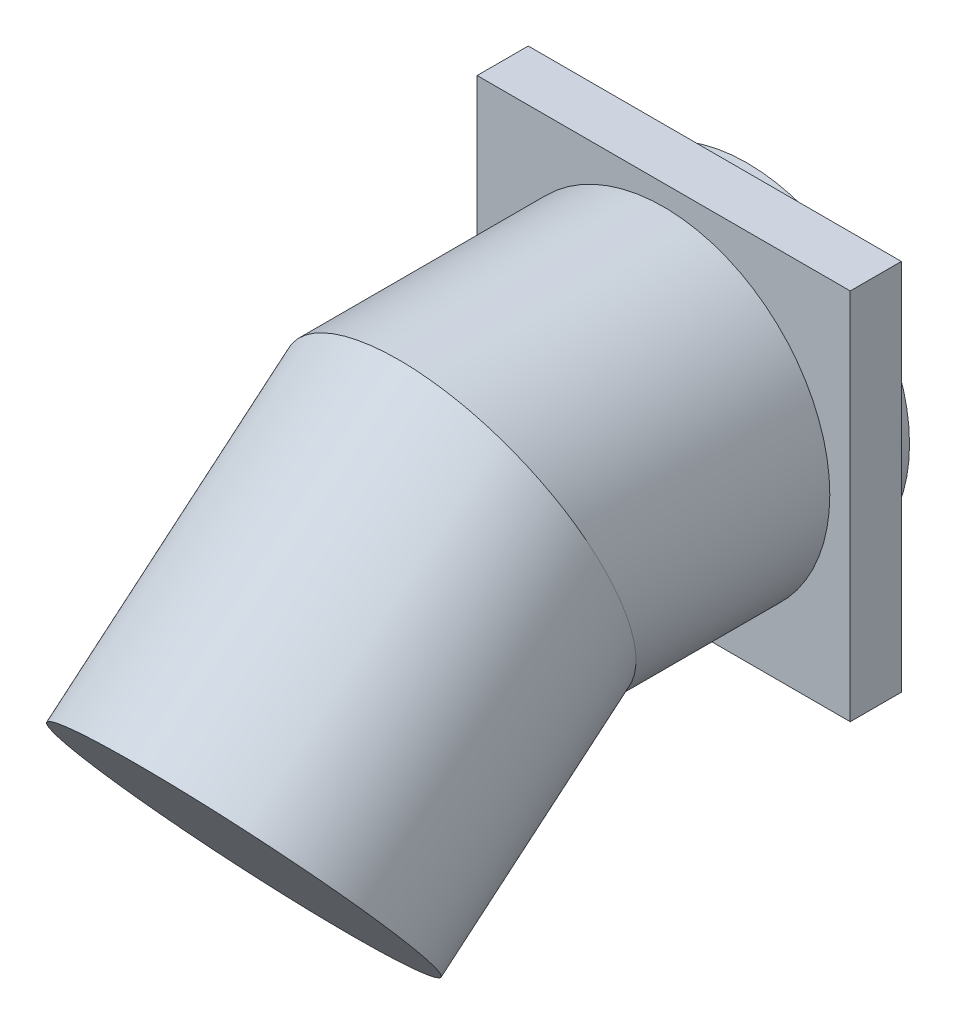
SolidWorks part; units mm, degrees
ref_plane "Front Plane" through (0, 0, 0) normal (0, 0, 1) x (1, 0, 0)
ref_plane "Top Plane" through (0, 0, 0) normal (0, 1, 0) x (1, 0, 0)
ref_plane "Right Plane" through (0, 0, 0) normal (1, 0, 0) x (0, 0, -1)
sketch "Sketch1" plane through (0, 0, 0) normal (0, 0, 1) x (1, 0, 0)
  line L1 (-73, 73) -> (73, 73)
  line L2 (-73, 73) -> (-73, -73)
  line L3 (-73, -73) -> (73, -73)
  line L4 (73, 73) -> (73, -73)
  dimension "D1" = 146
  dimension "D2" = 73
  dimension "D3" = 146
  dimension "D4" = 73
extrude "Boss-Extrude1" add sketch "Sketch1" along normal blind 20
sketch "Sketch2" plane through (0, 0, 0) normal (0, 0, -1) x (-1, 0, 0)
  circle A0 centre (0, 0) radius 63.5
  dimension "D1" = 127
extrude "Boss-Extrude2" add sketch "Sketch2" along normal blind 12.7
sketch "Sketch3" plane through (0, 0, 20) normal (0, 0, 1) x (1, 0, 0)
  circle A0 centre (0, 0) radius 65
  dimension "D1" = 130
sketch "Sketch4" plane through (0, 0, 0) normal (1, 0, 0) x (0, 0, -1)
  line L0 (-20, 0) -> (-100, 0)
  line L1 (-20, 65) -> (-20, -65) construction
  line L2 (17.985, 0) -> (-17.985, 0) construction
  line L3 (-100, 0) -> (-184.2649, -70.7066)
  dimension "D1" = 80
  dimension "D2" = 110
  dimension "D3" = 40
sweep "Sweep1" add profiles "Sketch3" path "Sketch4"
